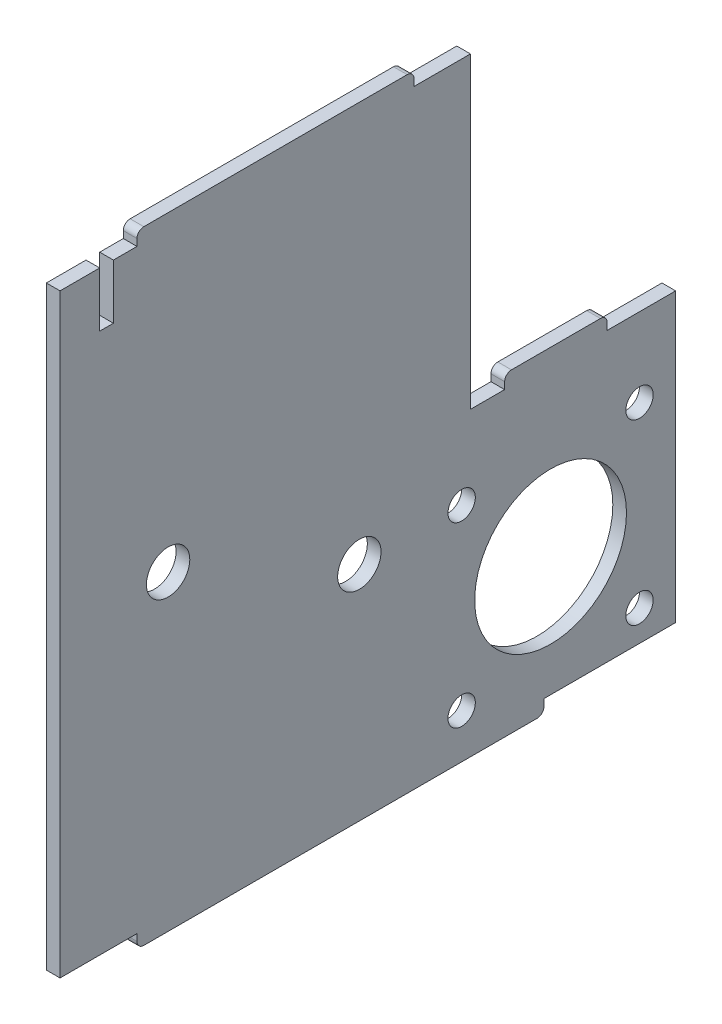
SolidWorks part; units mm, degrees
ref_plane "Front Plane" through (0, 0, 0) normal (0, 0, 1) x (1, 0, 0)
ref_plane "Top Plane" through (0, 0, 0) normal (0, 1, 0) x (1, 0, 0)
ref_plane "Right Plane" through (0, 0, 0) normal (1, 0, 0) x (0, 0, -1)
sketch "Sketch1" plane through (0, 0, 0) normal (1, 0, 0) x (0, 0, -1)
  line L0 (47.8012, -63.1311) -> (47.8012, -21.1311)
  line L1 (9.5507, 23.8689) -> (9.5507, 24.8689)
  line L2 (8.5507, 25.8689) -> (-29.9483, 25.8689)
  line L3 (-42.1988, -63.1311) -> (-42.1988, 23.8689)
  line L4 (17.8012, -21.1311) -> (17.8012, 23.8689)
  line L5 (-30.9483, -63.1311) -> (-30.9483, -64.1311)
  line L6 (-34.3988, 15.8689) -> (-36.3988, 15.8689)
  line L7 (47.8012, -63.1311) -> (28.5507, -63.1311)
  line L8 (-30.9483, 23.8689) -> (-34.3988, 23.8689)
  line L9 (-34.3988, 15.8689) -> (-34.3988, 23.8689)
  line L10 (-36.3988, 23.8689) -> (-42.1988, 23.8689)
  line L11 (36.8012, -19.1311) -> (23.8012, -19.1311)
  line L12 (28.5507, -63.1311) -> (28.5507, -64.1311)
  line L13 (-36.3988, 15.8689) -> (-36.3988, 23.8689)
  line L14 (17.8012, -21.1311) -> (22.8012, -21.1311)
  line L15 (9.5507, 23.8689) -> (17.8012, 23.8689)
  line L16 (-30.9483, 23.8689) -> (-30.9483, 24.8689)
  line L17 (22.8012, -21.1311) -> (22.8012, -20.1311)
  line L18 (-29.9483, -65.1311) -> (27.5507, -65.1311)
  line L19 (-42.1988, -63.1311) -> (-30.9483, -63.1311)
  line L20 (37.8012, -21.1311) -> (37.8012, -20.1311)
  line L21 (37.8012, -21.1311) -> (47.8012, -21.1311)
  arc A0 (-29.9483, -65.1311) -> (-30.9483, -64.1311) centre (-29.9483, -64.1311) cw
  circle A1 centre (-26.3988, -19.6311) radius 3.17
  circle A2 centre (29.5157, -45.6311) radius 11.1
  arc A3 (37.8012, -20.1311) -> (36.8012, -19.1311) centre (36.8012, -20.1311) ccw
  arc A4 (27.5507, -65.1311) -> (28.5507, -64.1311) centre (27.5507, -64.1311) ccw
  arc A5 (9.5507, 24.8689) -> (8.5507, 25.8689) centre (8.5507, 24.8689) ccw
  arc A6 (-30.9483, 24.8689) -> (-29.9483, 25.8689) centre (-29.9483, 24.8689) cw
  circle A7 centre (16.5157, -32.6311) radius 2
  circle A8 centre (42.5157, -32.6311) radius 2
  circle A9 centre (42.5157, -58.6311) radius 2
  circle A10 centre (16.5157, -58.6311) radius 2
  arc A11 (22.8012, -20.1311) -> (23.8012, -19.1311) centre (23.8012, -20.1311) cw
  circle A12 centre (1.5585, -32.6311) radius 3.17
  point P8 (47.8012, 23.8689)
  point P27 (17.8012, -63.1311)
  point P42 (9.5507, -26.1311)
  point P43 (47.8012, -26.1311)
extrude "Boss-Extrude2" add sketch "Sketch1" along normal blind 2
